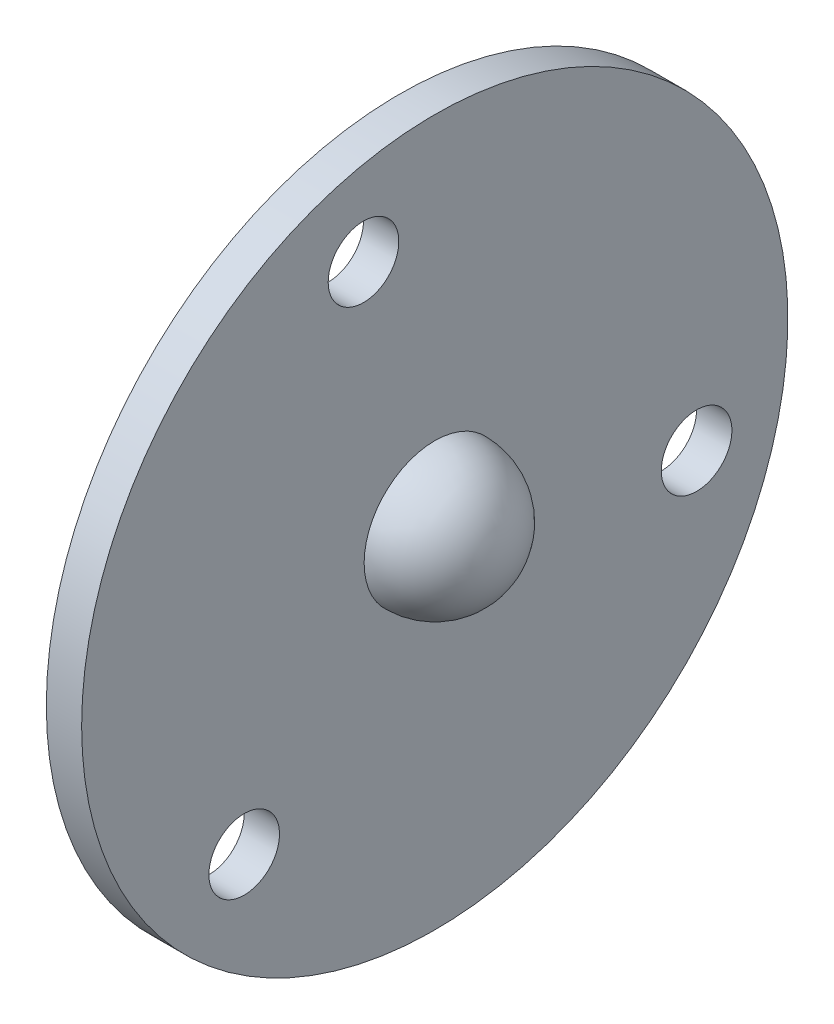
SolidWorks part; units mm, degrees
material "3.0205 (EN-AW 1200)"
ref_plane "Plan de face" through (0, 0, 0) normal (0, 0, 1) x (1, 0, 0)
ref_plane "Plan de dessus" through (0, 0, 0) normal (0, 1, 0) x (1, 0, 0)
ref_plane "Plan de droite" through (0, 0, 0) normal (1, 0, 0) x (0, 0, -1)
sketch "Esquisse2" plane through (0, 0, 0) normal (0, 1, 0) x (1, 0, 0)
  line L0 (-57.6693, 0) -> (51.116, 0) construction
  line L1 (-24.1963, 6) -> (-24.1963, 30)
  line L2 (-24.1963, 30) -> (-27.1963, 30)
  line L3 (-27.1963, 30) -> (-27.1963, 11)
  line L4 (-38.1963, 0) -> (-18.1963, 0)
  arc A0 (-38.1963, 0) -> (-27.1963, 11) centre (-27.1963, 0) cw
  arc A1 (-18.1963, 0) -> (-24.1963, 6) centre (-24.1963, 0) ccw
  dimension "D1" = 11
  dimension "D2" = 6
  dimension "D3" = 3
  dimension "D4" = 30
revolve "Révolution1" add sketch "Esquisse2" angle 360 about L0
sketch "Esquisse3" plane through (-27.1963, 0, 0) normal (-1, 0, 0) x (0, 0, 1)
  circle A0 centre (-22.2433, -5.8513) radius 3
  circle A2 centre (0, 0) radius 30 construction
  dimension "D1" = 6
  dimension "D2" = 23
extrude "Enlèv. mat.-Extru.1" cut sketch "Esquisse3" against normal blind 10
pattern_circular "Répétition circulaire1" count 3 over 360 about axis through (0, 0, 0) along (1, 0, 0) of "Enlèv. mat.-Extru.1"
